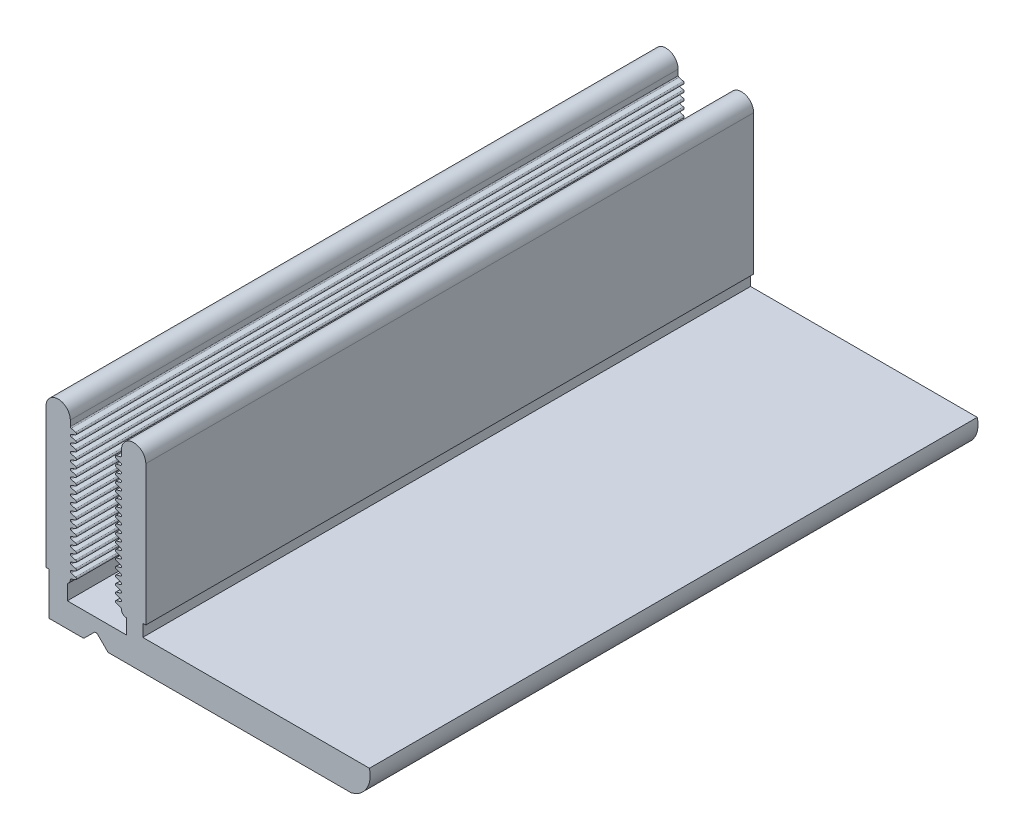
SolidWorks part; units mm, degrees
ref_plane "Спереди" through (0, 0, 0) normal (0, 0, 1) x (1, 0, 0)
ref_plane "Сверху" through (0, 0, 0) normal (0, 1, 0) x (1, 0, 0)
ref_plane "Справа" through (0, 0, 0) normal (1, 0, 0) x (0, 0, -1)
sketch "Эскиз1" plane through (0, 0, 0) normal (0, 0, 1) x (1, 0, 0)
  line L12 (1.7494, 2) -> (6.5975, 2)
  line L80 (3.9561, 0.8586) -> (3.1561, 0.0586)
  line L100 (2.0661, 10.8085) -> (2.4215, 10.7114)
  line L101 (2.0604, 10.384) -> (2.43, 10.5212)
  line L102 (2.0604, 10.9909) -> (2.43, 11.1281)
  line L104 (2.0604, 12.8116) -> (2.43, 12.9488)
  line L105 (2.0661, 11.4154) -> (2.4215, 11.3183)
  line L107 (3.0147, 0) -> (0.2427, 0)
  line L108 (2.0661, 7.774) -> (2.4215, 7.6769)
  line L109 (2.0604, 7.9564) -> (2.43, 8.0936)
  line L110 (2.0661, 8.3809) -> (2.4215, 8.2838)
  line L111 (2.0661, 10.2016) -> (2.4215, 10.1045)
  line L112 (2.0661, 8.9878) -> (2.4215, 8.8907)
  line L113 (2.0604, 8.5633) -> (2.43, 8.7005)
  line L114 (2.0604, 9.1702) -> (2.43, 9.3074)
  line L115 (2.0604, 9.7771) -> (2.43, 9.9143)
  line L116 (2.0661, 9.5947) -> (2.4215, 9.4976)
  line L117 (2.0661, 4.1326) -> (2.4215, 4.0355)
  line L118 (2.0604, 3.7081) -> (2.43, 3.8453)
  line L119 (2.0604, 4.315) -> (2.43, 4.4522)
  line L120 (2.0661, 4.7395) -> (2.4215, 4.6424)
  line L121 (2.0661, 5.3464) -> (2.4215, 5.2493)
  line L122 (2.0604, 5.5288) -> (2.43, 5.666)
  line L123 (2.0661, 5.9533) -> (2.4215, 5.8562)
  line L124 (2.0604, 4.9219) -> (2.43, 5.0591)
  line L125 (2.0661, 6.5602) -> (2.4215, 6.4631)
  line L126 (2.0604, 6.7426) -> (2.43, 6.8798)
  line L127 (2.0604, 6.1357) -> (2.43, 6.2729)
  line L128 (2.0604, 7.3495) -> (2.43, 7.4867)
  line L129 (2.0661, 7.1671) -> (2.4215, 7.07)
  line L131 (-0.0073, 3.5056) -> (0.2427, 3.5056)
  line L132 (0.2427, 3.5056) -> (0.2427, 2.0056)
  line L135 (-0.0073, 3.5056) -> (-0.0073, 15)
  line L136 (2.0604, 13.4185) -> (2.43, 13.5557)
  line L139 (0.2427, 2.0056) -> (0.2427, 0)
  line L140 (2.0661, 13.843) -> (2.4215, 13.7459)
  line L141 (1.9927, 15) -> (1.9927, 14.5393)
  line L142 (2.0661, 12.0223) -> (2.4215, 11.9252)
  line L143 (2.0661, 14.4499) -> (2.4215, 14.3528)
  line L144 (2.0604, 14.0254) -> (2.43, 14.1626)
  line L145 (2.0604, 11.5978) -> (2.43, 11.735)
  line L146 (2.0661, 12.6292) -> (2.4215, 12.5321)
  line L147 (2.0661, 13.2361) -> (2.4215, 13.139)
  line L148 (2.0604, 12.2047) -> (2.43, 12.3419)
  line L149 (4.2389, 0.8586) -> (5.0389, 0.0586)
  line L150 (6.1346, 12.2047) -> (5.765, 12.3419)
  line L151 (6.1289, 13.2361) -> (5.7735, 13.139)
  line L152 (6.1289, 12.6292) -> (5.7735, 12.5321)
  line L153 (6.1346, 11.5978) -> (5.765, 11.735)
  line L154 (6.1346, 14.0254) -> (5.765, 14.1626)
  line L155 (6.1289, 14.4499) -> (5.7735, 14.3528)
  line L156 (6.1289, 12.0223) -> (5.7735, 11.9252)
  line L157 (6.2023, 15) -> (6.2023, 14.5393)
  line L158 (6.1289, 13.843) -> (5.7735, 13.7459)
  line L159 (6.1346, 13.4185) -> (5.765, 13.5557)
  line L160 (8.2023, 3.5056) -> (8.2023, 15)
  line L161 (7.9523, 3.5056) -> (7.9523, 2.5)
  line L162 (8.2023, 3.5056) -> (7.9523, 3.5056)
  line L163 (6.5975, 3.22) -> (6.5975, 2)
  line L164 (6.1289, 7.1671) -> (5.7735, 7.07)
  line L165 (6.1346, 7.3495) -> (5.765, 7.4867)
  line L166 (6.1346, 6.1357) -> (5.765, 6.2729)
  line L167 (6.1346, 6.7426) -> (5.765, 6.8798)
  line L168 (6.1289, 6.5602) -> (5.7735, 6.4631)
  line L169 (6.1346, 4.9219) -> (5.765, 5.0591)
  line L170 (6.1289, 5.9533) -> (5.7735, 5.8562)
  line L171 (6.1346, 5.5288) -> (5.765, 5.666)
  line L172 (6.1289, 5.3464) -> (5.7735, 5.2493)
  line L173 (6.1289, 4.7395) -> (5.7735, 4.6424)
  line L174 (6.1346, 4.315) -> (5.765, 4.4522)
  line L175 (6.1346, 3.7081) -> (5.765, 3.8453)
  line L176 (6.1289, 4.1326) -> (5.7735, 4.0355)
  line L177 (6.1289, 9.5947) -> (5.7735, 9.4976)
  line L178 (6.1346, 9.7771) -> (5.765, 9.9143)
  line L179 (6.1346, 9.1702) -> (5.765, 9.3074)
  line L180 (6.1346, 8.5633) -> (5.765, 8.7005)
  line L181 (6.1289, 8.9878) -> (5.7735, 8.8907)
  line L182 (6.1289, 10.2016) -> (5.7735, 10.1045)
  line L183 (6.1289, 8.3809) -> (5.7735, 8.2838)
  line L184 (6.1346, 7.9564) -> (5.765, 8.0936)
  line L185 (6.1289, 7.774) -> (5.7735, 7.6769)
  line L187 (6.1289, 11.4154) -> (5.7735, 11.3183)
  line L188 (6.1346, 12.8116) -> (5.765, 12.9488)
  line L189 (6.1346, 10.9909) -> (5.765, 11.1281)
  line L190 (6.1346, 10.384) -> (5.765, 10.5212)
  line L191 (6.1289, 10.8085) -> (5.7735, 10.7114)
  line L192 (25.0975, 0) -> (17.5, 0)
  line L195 (5.1803, 0) -> (17.5, 0)
  line L196 (1.7494, 3.2504) -> (1.7494, 2)
  line L200 (16.2835, 2.5) -> (7.9523, 2.5)
  line L201 (16.2835, 2.5) -> (26.5975, 2.5)
  arc A91 (4.2389, 0.8586) -> (3.9561, 0.8586) centre (4.0975, 0.7172) ccw
  arc A94 (2.43, 3.8453) -> (2.4215, 4.0355) centre (2.3952, 3.939) ccw
  arc A95 (2.43, 4.4522) -> (2.4215, 4.6424) centre (2.3952, 4.5459) ccw
  arc A96 (2.43, 5.0591) -> (2.4215, 5.2493) centre (2.3952, 5.1528) ccw
  arc A97 (3.0147, 0) -> (3.1561, 0.0586) centre (3.0147, 0.2) ccw
  arc A98 (2.43, 7.4867) -> (2.4215, 7.6769) centre (2.3952, 7.5804) ccw
  arc A99 (2.43, 8.0936) -> (2.4215, 8.2838) centre (2.3952, 8.1873) ccw
  arc A100 (1.9927, 10.8979) -> (2.0604, 10.9909) centre (2.0965, 10.8935) cw
  arc A101 (2.43, 10.5212) -> (2.4215, 10.7114) centre (2.3952, 10.6149) ccw
  arc A102 (2.0661, 10.8085) -> (1.9927, 10.8979) centre (2.0924, 10.905) cw
  arc A103 (2.43, 9.9143) -> (2.4215, 10.1045) centre (2.3952, 10.008) ccw
  arc A104 (2.43, 9.3074) -> (2.4215, 9.4976) centre (2.3952, 9.4011) ccw
  arc A105 (2.43, 8.7005) -> (2.4215, 8.8907) centre (2.3952, 8.7942) ccw
  arc A106 (2.0661, 11.4154) -> (1.9927, 11.5048) centre (2.0924, 11.5119) cw
  arc A107 (2.43, 11.1281) -> (2.4215, 11.3183) centre (2.3952, 11.2218) ccw
  arc A108 (2.43, 5.666) -> (2.4215, 5.8562) centre (2.3952, 5.7597) ccw
  arc A109 (2.43, 6.2729) -> (2.4215, 6.4631) centre (2.3952, 6.3666) ccw
  arc A110 (2.43, 6.8798) -> (2.4215, 7.07) centre (2.3952, 6.9735) ccw
  arc A113 (2.0661, 7.774) -> (1.9927, 7.8634) centre (2.0924, 7.8705) cw
  arc A114 (2.0661, 8.3809) -> (1.9927, 8.4703) centre (2.0924, 8.4774) cw
  arc A115 (1.9927, 7.8634) -> (2.0604, 7.9564) centre (2.0965, 7.859) cw
  arc A116 (2.0661, 9.5947) -> (1.9927, 9.6841) centre (2.0924, 9.6912) cw
  arc A117 (2.0661, 8.9878) -> (1.9927, 9.0772) centre (2.0924, 9.0843) cw
  arc A118 (1.9927, 9.0772) -> (2.0604, 9.1702) centre (2.0965, 9.0728) cw
  arc A119 (2.0661, 10.2016) -> (1.9927, 10.291) centre (2.0924, 10.2981) cw
  arc A120 (1.9927, 8.4703) -> (2.0604, 8.5633) centre (2.0965, 8.4659) cw
  arc A121 (1.9927, 10.291) -> (2.0604, 10.384) centre (2.0965, 10.2866) cw
  arc A122 (1.9927, 9.6841) -> (2.0604, 9.7771) centre (2.0965, 9.6797) cw
  arc A123 (1.9927, 3.6152) -> (1.7494, 3.2504) centre (1.5975, 3.6152) cw
  arc A124 (2.0661, 4.1326) -> (1.9927, 4.2221) centre (2.0924, 4.2291) cw
  arc A125 (1.9927, 3.6152) -> (2.0604, 3.7081) centre (2.0965, 3.6107) cw
  arc A126 (1.9927, 4.2221) -> (2.0604, 4.315) centre (2.0965, 4.2176) cw
  arc A127 (2.0661, 4.7395) -> (1.9927, 4.829) centre (2.0924, 4.836) cw
  arc A128 (1.9927, 5.4359) -> (2.0604, 5.5288) centre (2.0965, 5.4314) cw
  arc A129 (2.0661, 5.3464) -> (1.9927, 5.4359) centre (2.0924, 5.4429) cw
  arc A130 (2.0661, 5.9533) -> (1.9927, 6.0428) centre (2.0924, 6.0498) cw
  arc A131 (1.9927, 4.829) -> (2.0604, 4.9219) centre (2.0965, 4.8245) cw
  arc A132 (1.9927, 6.6497) -> (2.0604, 6.7426) centre (2.0965, 6.6452) cw
  arc A133 (1.9927, 6.0428) -> (2.0604, 6.1357) centre (2.0965, 6.0383) cw
  arc A134 (2.0661, 6.5602) -> (1.9927, 6.6497) centre (2.0924, 6.6567) cw
  arc A135 (1.9927, 7.2566) -> (2.0604, 7.3495) centre (2.0965, 7.2521) cw
  arc A136 (2.0661, 7.1671) -> (1.9927, 7.2566) centre (2.0924, 7.2636) cw
  arc A138 (-0.0073, 15) -> (1.9927, 15) centre (0.9927, 15) cw
  arc A139 (1.9927, 11.5048) -> (2.0604, 11.5978) centre (2.0965, 11.5004) cw
  arc A140 (2.43, 14.1626) -> (2.4215, 14.3528) centre (2.3952, 14.2563) ccw
  arc A141 (2.0661, 12.0223) -> (1.9927, 12.1117) centre (2.0924, 12.1188) cw
  arc A142 (2.0661, 13.2361) -> (1.9927, 13.3255) centre (2.0924, 13.3326) cw
  arc A143 (2.43, 13.5557) -> (2.4215, 13.7459) centre (2.3952, 13.6494) ccw
  arc A144 (2.0661, 12.6292) -> (1.9927, 12.7186) centre (2.0924, 12.7257) cw
  arc A145 (2.43, 11.735) -> (2.4215, 11.9252) centre (2.3952, 11.8287) ccw
  arc A146 (1.9927, 12.1117) -> (2.0604, 12.2047) centre (2.0965, 12.1073) cw
  arc A147 (1.9927, 13.3255) -> (2.0604, 13.4185) centre (2.0965, 13.3211) cw
  arc A148 (1.9927, 12.7186) -> (2.0604, 12.8116) centre (2.0965, 12.7142) cw
  arc A149 (2.0661, 14.4499) -> (1.9927, 14.5393) centre (2.0924, 14.5464) cw
  arc A150 (2.43, 12.9488) -> (2.4215, 13.139) centre (2.3952, 13.0425) ccw
  arc A151 (2.43, 12.3419) -> (2.4215, 12.5321) centre (2.3952, 12.4356) ccw
  arc A152 (2.0661, 13.843) -> (1.9927, 13.9324) centre (2.0924, 13.9395) cw
  arc A153 (1.9927, 13.9324) -> (2.0604, 14.0254) centre (2.0965, 13.928) cw
  arc A154 (5.1803, 0) -> (5.0389, 0.0586) centre (5.1803, 0.2) cw
  arc A155 (6.2023, 13.9324) -> (6.1346, 14.0254) centre (6.0985, 13.928) ccw
  arc A156 (6.1289, 13.843) -> (6.2023, 13.9324) centre (6.1025, 13.9395) ccw
  arc A157 (5.765, 12.3419) -> (5.7735, 12.5321) centre (5.7998, 12.4356) cw
  arc A158 (5.765, 12.9488) -> (5.7735, 13.139) centre (5.7998, 13.0425) cw
  arc A159 (6.1289, 14.4499) -> (6.2023, 14.5393) centre (6.1025, 14.5464) ccw
  arc A160 (6.2023, 12.7186) -> (6.1346, 12.8116) centre (6.0985, 12.7142) ccw
  arc A161 (6.2023, 13.3255) -> (6.1346, 13.4185) centre (6.0985, 13.3211) ccw
  arc A162 (6.2023, 12.1117) -> (6.1346, 12.2047) centre (6.0985, 12.1073) ccw
  arc A163 (5.765, 11.735) -> (5.7735, 11.9252) centre (5.7998, 11.8287) cw
  arc A164 (6.1289, 12.6292) -> (6.2023, 12.7186) centre (6.1025, 12.7257) ccw
  arc A165 (5.765, 13.5557) -> (5.7735, 13.7459) centre (5.7998, 13.6494) cw
  arc A166 (6.1289, 13.2361) -> (6.2023, 13.3255) centre (6.1025, 13.3326) ccw
  arc A167 (6.1289, 12.0223) -> (6.2023, 12.1117) centre (6.1025, 12.1188) ccw
  arc A168 (5.765, 14.1626) -> (5.7735, 14.3528) centre (5.7998, 14.2563) cw
  arc A169 (6.2023, 11.5048) -> (6.1346, 11.5978) centre (6.0985, 11.5004) ccw
  arc A170 (8.2023, 15) -> (6.2023, 15) centre (7.2023, 15) ccw
  arc A171 (6.1289, 7.1671) -> (6.2023, 7.2566) centre (6.1025, 7.2636) ccw
  arc A172 (6.2023, 7.2566) -> (6.1346, 7.3495) centre (6.0985, 7.2521) ccw
  arc A173 (6.1289, 6.5602) -> (6.2023, 6.6497) centre (6.1025, 6.6567) ccw
  arc A174 (6.2023, 6.0428) -> (6.1346, 6.1357) centre (6.0985, 6.0383) ccw
  arc A175 (6.2023, 6.6497) -> (6.1346, 6.7426) centre (6.0985, 6.6452) ccw
  arc A176 (6.2023, 4.829) -> (6.1346, 4.9219) centre (6.0985, 4.8245) ccw
  arc A177 (6.1289, 5.9533) -> (6.2023, 6.0428) centre (6.1025, 6.0498) ccw
  arc A178 (6.1289, 5.3464) -> (6.2023, 5.4359) centre (6.1025, 5.4429) ccw
  arc A179 (6.2023, 5.4359) -> (6.1346, 5.5288) centre (6.0985, 5.4314) ccw
  arc A180 (6.1289, 4.7395) -> (6.2023, 4.829) centre (6.1025, 4.836) ccw
  arc A181 (6.2023, 4.2221) -> (6.1346, 4.315) centre (6.0985, 4.2176) ccw
  arc A182 (6.2023, 3.6152) -> (6.1346, 3.7081) centre (6.0985, 3.6107) ccw
  arc A183 (6.1289, 4.1326) -> (6.2023, 4.2221) centre (6.1025, 4.2291) ccw
  arc A184 (6.2023, 3.6152) -> (6.5975, 3.22) centre (6.5975, 3.6152) ccw
  arc A185 (6.2023, 9.6841) -> (6.1346, 9.7771) centre (6.0985, 9.6797) ccw
  arc A186 (6.2023, 10.291) -> (6.1346, 10.384) centre (6.0985, 10.2866) ccw
  arc A187 (6.2023, 8.4703) -> (6.1346, 8.5633) centre (6.0985, 8.4659) ccw
  arc A188 (6.1289, 10.2016) -> (6.2023, 10.291) centre (6.1025, 10.2981) ccw
  arc A189 (6.2023, 9.0772) -> (6.1346, 9.1702) centre (6.0985, 9.0728) ccw
  arc A190 (6.1289, 8.9878) -> (6.2023, 9.0772) centre (6.1025, 9.0843) ccw
  arc A191 (6.1289, 9.5947) -> (6.2023, 9.6841) centre (6.1025, 9.6912) ccw
  arc A192 (6.2023, 7.8634) -> (6.1346, 7.9564) centre (6.0985, 7.859) ccw
  arc A193 (6.1289, 8.3809) -> (6.2023, 8.4703) centre (6.1025, 8.4774) ccw
  arc A194 (6.1289, 7.774) -> (6.2023, 7.8634) centre (6.1025, 7.8705) ccw
  arc A195 (5.765, 6.8798) -> (5.7735, 7.07) centre (5.7998, 6.9735) cw
  arc A196 (5.765, 6.2729) -> (5.7735, 6.4631) centre (5.7998, 6.3666) cw
  arc A197 (5.765, 5.666) -> (5.7735, 5.8562) centre (5.7998, 5.7597) cw
  arc A198 (5.765, 11.1281) -> (5.7735, 11.3183) centre (5.7998, 11.2218) cw
  arc A199 (6.1289, 11.4154) -> (6.2023, 11.5048) centre (6.1025, 11.5119) ccw
  arc A200 (5.765, 8.7005) -> (5.7735, 8.8907) centre (5.7998, 8.7942) cw
  arc A201 (5.765, 9.3074) -> (5.7735, 9.4976) centre (5.7998, 9.4011) cw
  arc A202 (5.765, 9.9143) -> (5.7735, 10.1045) centre (5.7998, 10.008) cw
  arc A203 (6.1289, 10.8085) -> (6.2023, 10.8979) centre (6.1025, 10.905) ccw
  arc A204 (5.765, 10.5212) -> (5.7735, 10.7114) centre (5.7998, 10.6149) cw
  arc A205 (6.2023, 10.8979) -> (6.1346, 10.9909) centre (6.0985, 10.8935) ccw
  arc A206 (5.765, 8.0936) -> (5.7735, 8.2838) centre (5.7998, 8.1873) cw
  arc A207 (5.765, 7.4867) -> (5.7735, 7.6769) centre (5.7998, 7.5804) cw
  arc A208 (5.765, 5.0591) -> (5.7735, 5.2493) centre (5.7998, 5.1528) cw
  arc A209 (5.765, 4.4522) -> (5.7735, 4.6424) centre (5.7998, 4.5459) cw
  arc A210 (5.765, 3.8453) -> (5.7735, 4.0355) centre (5.7998, 3.939) cw
  arc A212 (26.5975, 2.5) -> (25.0975, 0) centre (24.5975, 2) cw
  point P75 (7, 10.9962)
  point P77 (1.195, 10.9962)
  point P329 (4.0975, 2)
extrude "Бобышка-Вытянуть2" add sketch "Эскиз1" along normal blind 50
